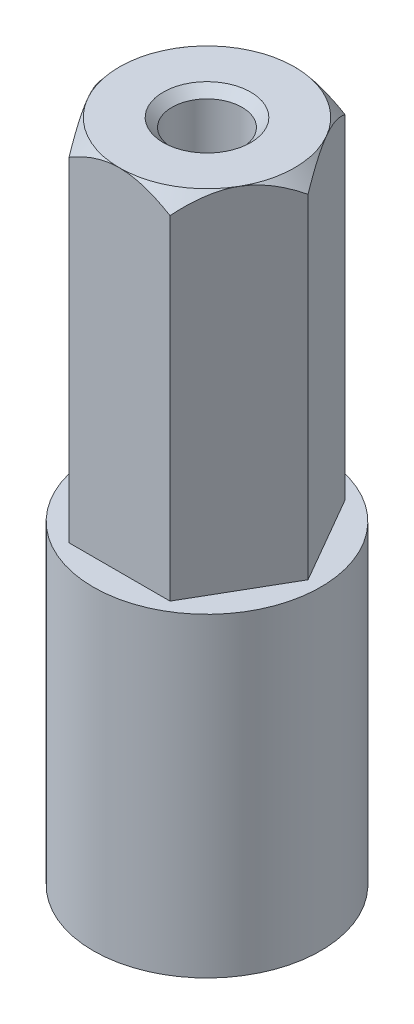
SolidWorks part; units mm, degrees
ref_plane "Ön Düzlem" through (0, 0, 0) normal (0, 0, 1) x (1, 0, 0)
ref_plane "Üst Düzlem" through (0, 0, 0) normal (0, 1, 0) x (1, 0, 0)
ref_plane "Sağ Düzlem" through (0, 0, 0) normal (1, 0, 0) x (0, 0, -1)
sketch "Sketch1" plane through (0, 0, 0) normal (0, 1, 0) x (1, 0, 0)
  circle A0 centre (0, 0) radius 3.25
  circle A1 centre (0, 0) radius 1.5
  dimension "D1" = 6.5
  dimension "D2" = 3
extrude "Boss-Extrude1" add sketch "Sketch1" along normal blind 6
sketch "Sketch2" plane through (0, 6, 0) normal (0, 1, 0) x (1, 0, 0)
  circle A0 centre (0, 0) radius 3.25
  circle A1 centre (0, 0) radius 3.25 construction
extrude "Boss-Extrude2" add sketch "Sketch2" along normal blind 3
sketch "Sketch3" plane through (0, 9, 0) normal (0, 1, 0) x (1, 0, 0)
  line L1 (2.8868, 0) -> (1.4434, 2.5)
  line L2 (1.4434, 2.5) -> (-1.4434, 2.5)
  line L3 (-1.4434, 2.5) -> (-2.8868, 0)
  line L4 (-2.8868, 0) -> (-1.4434, -2.5)
  line L5 (-1.4434, -2.5) -> (1.4434, -2.5)
  line L6 (1.4434, -2.5) -> (2.8868, 0)
  circle A0 centre (0, 0) radius 2.5 construction
  dimension "D1" = 5
extrude "Boss-Extrude3" add sketch "Sketch3" along normal blind 10
sketch "Sketch4" plane through (0, 19, 0) normal (0, 1, 0) x (1, 0, 0)
  line L0 (2.8868, 0) -> (1.4434, 2.5) construction
  line L1 (-1.4434, 2.5) -> (-2.8868, 0) construction
  line L2 (-2.8868, 0) -> (-1.4434, -2.5) construction
  circle A0 centre (0, 0) radius 2.5
extrude "Cut-Extrude1" cut sketch "Sketch4" against normal blind 10 draft 40 flip side to cut
sketch "Sketch5" plane through (0, 19, 0) normal (0, 1, 0) x (1, 0, 0)
  point P0 (0, 0)
hole_wizard "CSK for M2.5 Flat Head Machine Screw1" positions "Sketch5" profile "Sketch7" countersink size "M2.5" standard "ANSI Metric"
sketch "Sketch7" plane through (0, 19, 0) normal (1, 0, 0) x (0, 0, 1)
  line L0 (0, 0) -> (0, 6.6009)
  line L1 (0, 6.6009) -> (1, 6)
  line L2 (1, 6) -> (1, 0.25)
  line L3 (1, 0.25) -> (1.25, 0)
  line L5 (1.25, 0) -> (0, 0)
  line L6 (-1, 0.25) -> (-1.25, 0) construction
  line L10 (0, 6.6009) -> (-1, 6) construction
  line L11 (0, -6.35) -> (0, 107.95) construction
  dimension "Hole Dia." = 2
  dimension "Hole Depth" = 6
  dimension "Near C'Sink Dia." = 2.5
  dimension "Near C'Sink Angle" = 90
  dimension "Drill Angle" = 118
sketch "Sketch8" plane through (0, 0, 0) normal (1, 0, 0) x (0, 0, -1)
  line L0 (0, 2.5) -> (0, 0) construction
  line L1 (0, 5.5) -> (0, 9) construction
  circle A0 centre (0, 4) radius 1.5
  dimension "D1" = 3
  dimension "D2" = 3.5
extrude "Cut-Extrude2" cut sketch "Sketch8" against normal through all
